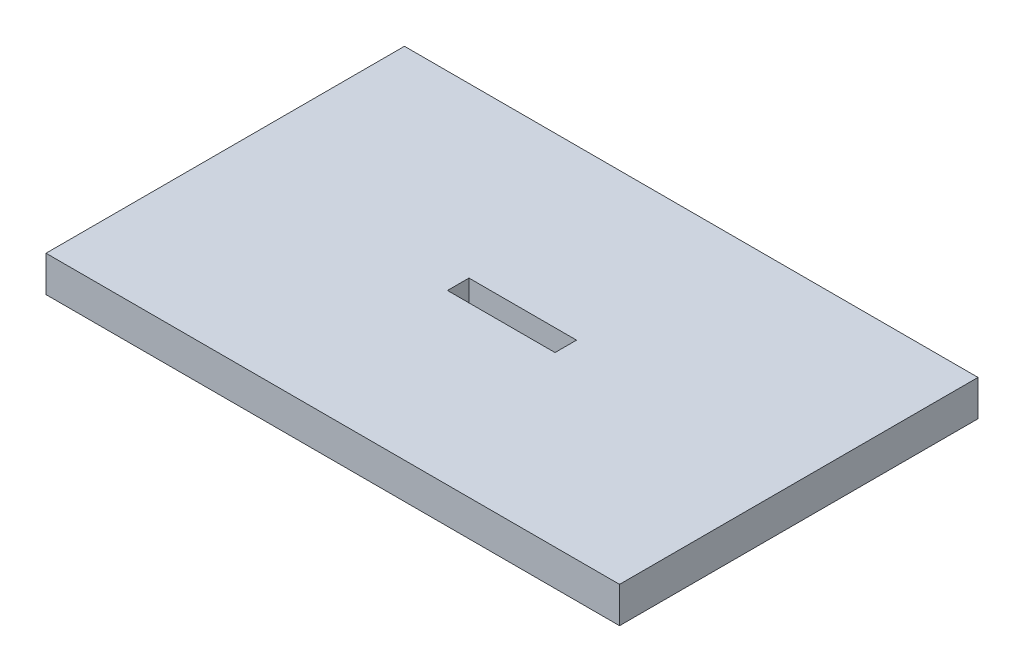
SolidWorks part; units mm, degrees
ref_plane "Спереди" through (0, 0, 0) normal (0, 0, 1) x (1, 0, 0)
ref_plane "Сверху" through (0, 0, 0) normal (0, 1, 0) x (1, 0, 0)
ref_plane "Справа" through (0, 0, 0) normal (1, 0, 0) x (0, 0, -1)
sketch "Эскиз1" plane through (0, 0, 0) normal (0, 1, 0) x (1, 0, 0)
  line L1 (-80, -50) -> (80, -50)
  line L2 (-80, -50) -> (-80, 50)
  line L3 (-80, 50) -> (80, 50)
  line L4 (80, -50) -> (80, 50)
  line L5 (-80, -50) -> (80, 50) construction
  line L6 (-80, 50) -> (80, -50) construction
  line L7 (-15, -3) -> (15, -3)
  line L8 (-15, -3) -> (-15, 3)
  line L9 (-15, 3) -> (15, 3)
  line L10 (15, -3) -> (15, 3)
  line L11 (-15, -3) -> (15, 3) construction
  line L12 (-15, 3) -> (15, -3) construction
  point P0 (0, 0)
  point P6 (0, 0)
  dimension "D1" = 160
  dimension "D2" = 100
  dimension "D3" = 30
  dimension "D4" = 6
extrude "Бобышка-Вытянуть1" add sketch "Эскиз1" along normal blind 10
